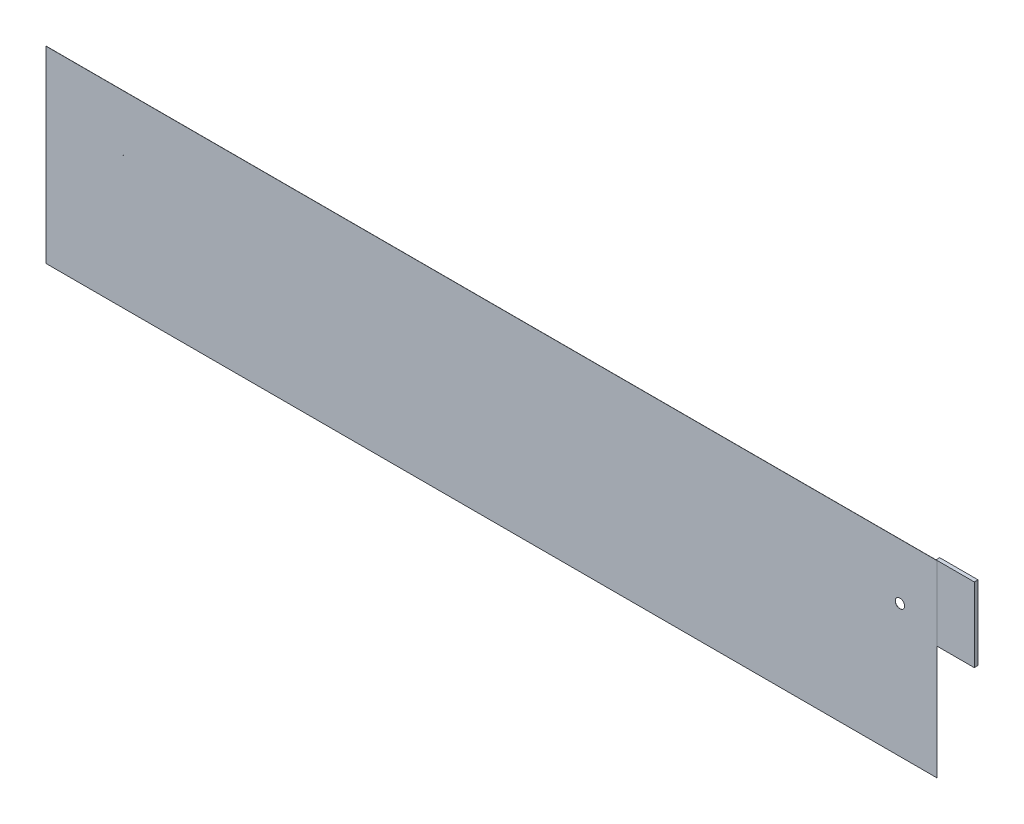
SolidWorks part; units mm, degrees
ref_plane "Front" through (0, 0, 0) normal (0, 0, 1) x (1, 0, 0)
ref_plane "Top" through (0, 0, 0) normal (0, 1, 0) x (1, 0, 0)
ref_plane "Right" through (0, 0, 0) normal (1, 0, 0) x (0, 0, -1)
sketch "Sketch1" plane through (0, 0, 0) normal (0, 0, 1) x (1, 0, 0)
  line L0 (0, 90.678) -> (609.6, 90.678) construction
  line L1 (0, 0) -> (609.6, 0)
  line L2 (0, 0) -> (0, 128.778)
  line L3 (0, 128.778) -> (609.6, 128.778)
  line L4 (609.6, 0) -> (609.6, 128.778)
  circle A0 centre (52.9747, 90.678) radius 0.1748
  circle A1 centre (584.2, 90.678) radius 3.175
  dimension "D4" = 25.4
  dimension "D5" = 6.35
  dimension "D1" = 128.778
  dimension "D2" = 609.6
  dimension "D3" = 38.1
extrude "Boss-Extrude1" add sketch "Sketch1" along normal blind 0.1
sketch "Sketch2" plane through (0, 0, 0) normal (0, 0, -1) x (-1, 0, 0)
  line L1 (-609.6, 128.778) -> (-635, 128.778)
  line L2 (-609.6, 128.778) -> (-609.6, 77.978)
  line L3 (-609.6, 77.978) -> (-635, 77.978)
  line L4 (-635, 128.778) -> (-635, 77.978)
  line L5 (-609.6, 128.778) -> (-608.8062, 128.778)
  line L6 (-609.6, 128.778) -> (-609.6, 77.978)
  line L7 (-609.6, 77.978) -> (-608.8062, 77.978)
  line L8 (-608.8062, 128.778) -> (-608.8062, 77.978)
  point P8 (-762, 77.4095)
  line M7 (0, 128.778) -> (-609.6, 128.778)
  line M8 (-609.6, 128.778) -> (-609.6, 0)
  dimension "D1" = 50.8
  dimension "D2" = 25.4
  dimension "D3" = 0.7937
extrude "Boss-Extrude2" add sketch "Sketch2" along normal blind 2.54 contours L1 L4 L3 M8 | L8 L7 M7 M8
